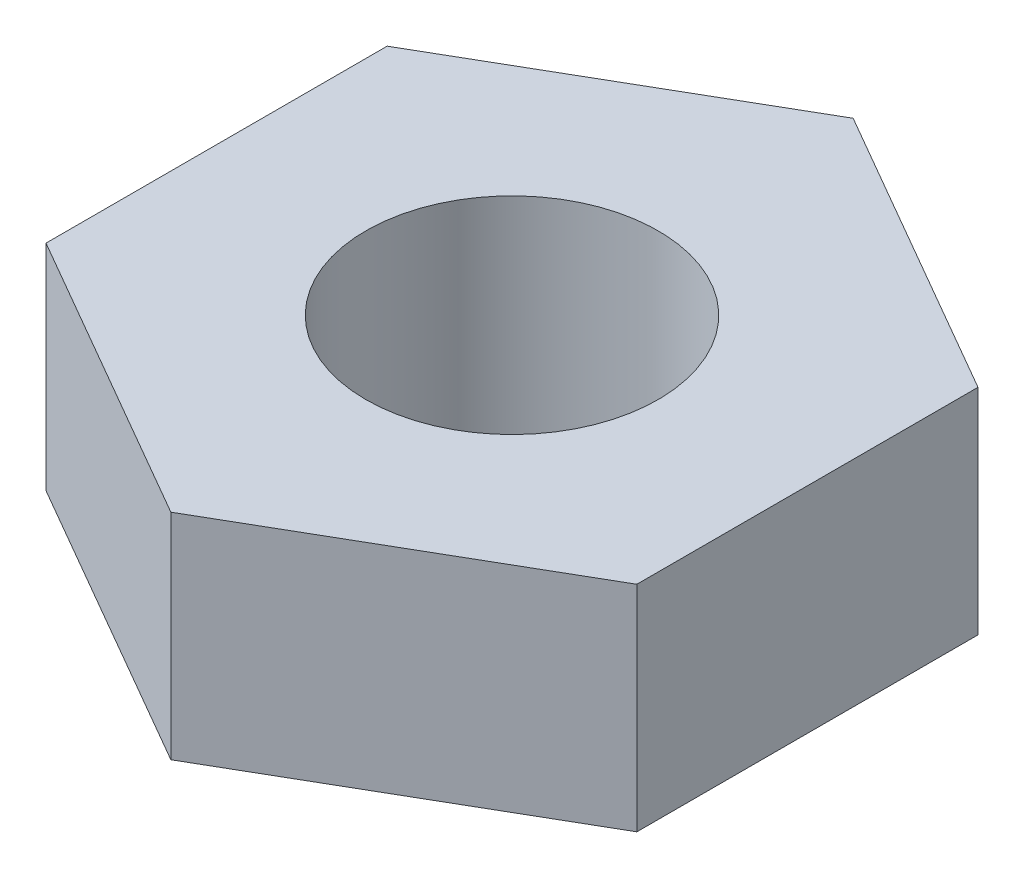
SolidWorks part; units mm, degrees
ref_plane "Front Plane" through (0, 0, 0) normal (0, 0, 1) x (1, 0, 0)
ref_plane "Top Plane" through (0, 0, 0) normal (0, 1, 0) x (1, 0, 0)
ref_plane "Right Plane" through (0, 0, 0) normal (1, 0, 0) x (0, 0, -1)
sketch "Sketch1" plane through (0, 0, 0) normal (0, 1, 0) x (1, 0, 0)
  line L1 (17.0331, -5.2281) -> (17.0331, 29.7719)
  line L2 (17.0331, 29.7719) -> (-13.2778, 47.2719)
  line L3 (-13.2778, 47.2719) -> (-43.5887, 29.7719)
  line L4 (-43.5887, 29.7719) -> (-43.5887, -5.2281)
  line L5 (-43.5887, -5.2281) -> (-13.2778, -22.7281)
  line L6 (-13.2778, -22.7281) -> (17.0331, -5.2281)
  circle A0 centre (-13.2778, 12.2719) radius 30.3109 construction
  circle A1 centre (-13.2778, 12.2719) radius 15
  dimension "D2" = 30
  dimension "D1" = 35
extrude "Boss-Extrude1" add sketch "Sketch1" along normal blind 22
scale "Scale1" scale about centroid uniform scaling yes scale factor 0.1
